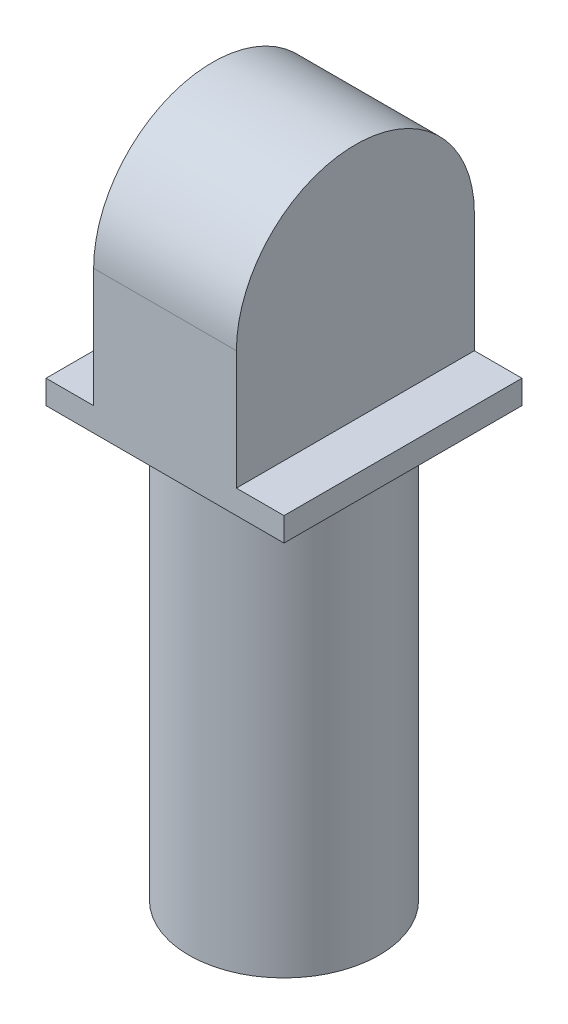
SolidWorks part; units mm, degrees
ref_plane "Front" through (0, 0, 0) normal (0, 0, 1) x (1, 0, 0)
ref_plane "Top" through (0, 0, 0) normal (0, 1, 0) x (1, 0, 0)
ref_plane "Right" through (0, 0, 0) normal (1, 0, 0) x (0, 0, -1)
sketch "草图1" plane through (0, 0, 0) normal (0, 1, 0) x (1, 0, 0)
  line L1 (-5, -5) -> (5, -5)
  line L2 (-5, -5) -> (-5, 5)
  line L3 (-5, 5) -> (5, 5)
  line L4 (5, -5) -> (5, 5)
  dimension "D1" = 10
  dimension "D2" = 10
  dimension "D3" = 5
  dimension "D4" = 5
extrude "凸台-拉伸1" add sketch "草图1" along normal blind 11
sketch "草图2" plane through (0, 0, 0) normal (0, -1, 0) x (1, 0, 0)
  circle A0 centre (0, 0) radius 4
extrude "凸台-拉伸2" add sketch "草图2" along normal blind 18
sketch "草图3" plane through (0, 0, 5) normal (0, 0, 1) x (1, 0, 0)
  line L0 (5, 11) -> (5, 0) construction
  line L1 (-5, 11) -> (-3, 11)
  line L2 (-5, 11) -> (-5, 1)
  line L3 (-5, 1) -> (-3, 1)
  line L4 (5, 11) -> (5, 1)
  line L5 (3, 11) -> (5, 11)
  line L7 (-3, 11) -> (-3, 1)
  line L9 (3, 11) -> (3, 1)
  line L10 (3, 1) -> (5, 1)
  dimension "D1" = 10
  dimension "D2" = 6
  dimension "D3" = 3
extrude "切除-拉伸1" cut sketch "草图3" against normal blind 46
sketch "草图4" plane through (3, 0, 0) normal (1, 0, 0) x (0, 0, -1)
  line L2 (-5, 6) -> (-5, 15.4362)
  line L3 (-5, 15.4362) -> (5, 15.4362)
  line L4 (5, 6) -> (5, 15.4362)
  arc A0 (5, 6) -> (-5, 6) centre (0, 6) ccw
extrude "切除-拉伸2" cut sketch "草图4" against normal blind 46
